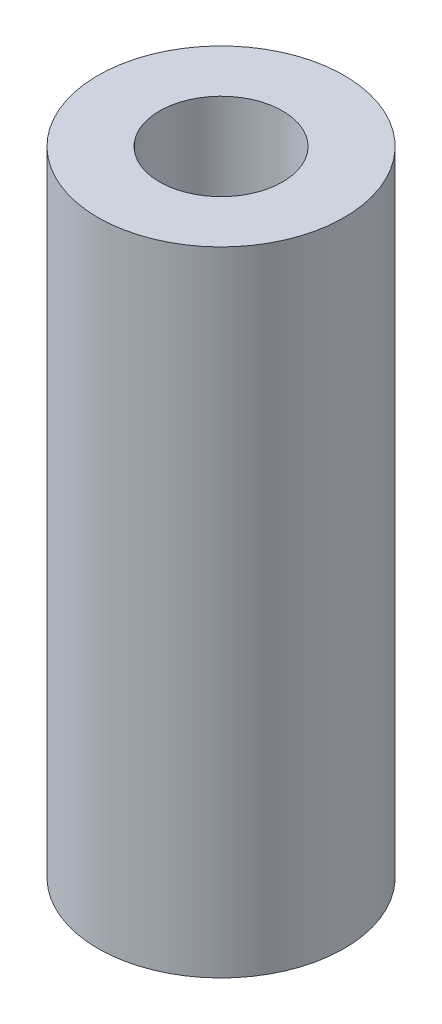
SolidWorks part; units mm, degrees
ref_plane "Front Plane" through (0, 0, 0) normal (0, 0, 1) x (1, 0, 0)
ref_plane "Top Plane" through (0, 0, 0) normal (0, 1, 0) x (1, 0, 0)
ref_plane "Right Plane" through (0, 0, 0) normal (1, 0, 0) x (0, 0, -1)
sketch "Sketch1" plane through (0, 0, 0) normal (0, 1, 0) x (1, 0, 0)
  circle A0 centre (0, 0) radius 3.5
  circle A1 centre (0, 0) radius 1.75
  dimension "D1" = 7
  dimension "D2" = 3.5
extrude "Boss-Extrude1" add sketch "Sketch1" along normal blind 18
